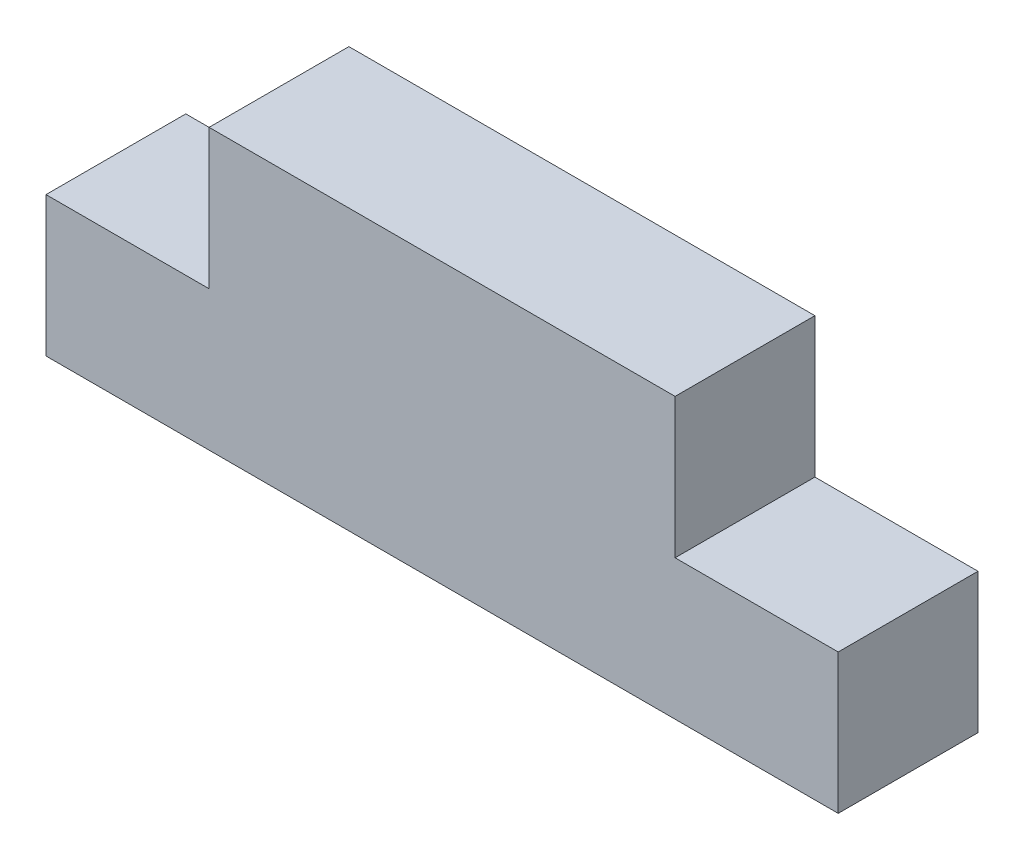
SolidWorks part; units mm, degrees
ref_plane "Plano frontal" through (0, 0, 0) normal (0, 0, 1) x (1, 0, 0)
ref_plane "Plano superior" through (0, 0, 0) normal (0, 1, 0) x (1, 0, 0)
ref_plane "Plano direito" through (0, 0, 0) normal (1, 0, 0) x (0, 0, -1)
sketch "Esboço1" plane through (0, 0, 0) normal (0, 0, 1) x (1, 0, 0)
  line L0 (7, 6) -> (7, 12)
  line L1 (0, 0) -> (34, 0)
  line L2 (0, 0) -> (0, 12)
  line L3 (0, 12) -> (34, 12)
  line L4 (34, 0) -> (34, 12)
  line L5 (0, 12) -> (6, 12)
  line L6 (0, 12) -> (0, 6)
  line L7 (0, 6) -> (7, 6)
  line L9 (34, 12) -> (28, 12)
  line L10 (34, 12) -> (34, 6)
  line L11 (34, 6) -> (27, 6)
  line L13 (27, 6) -> (27, 12)
  dimension "D1" = 12
  dimension "D2" = 7
  dimension "D3" = 6
  dimension "D4" = 20
  dimension "D5" = 7
extrude "Ressalto-extrusão1" add sketch "Esboço1" along normal blind 6
